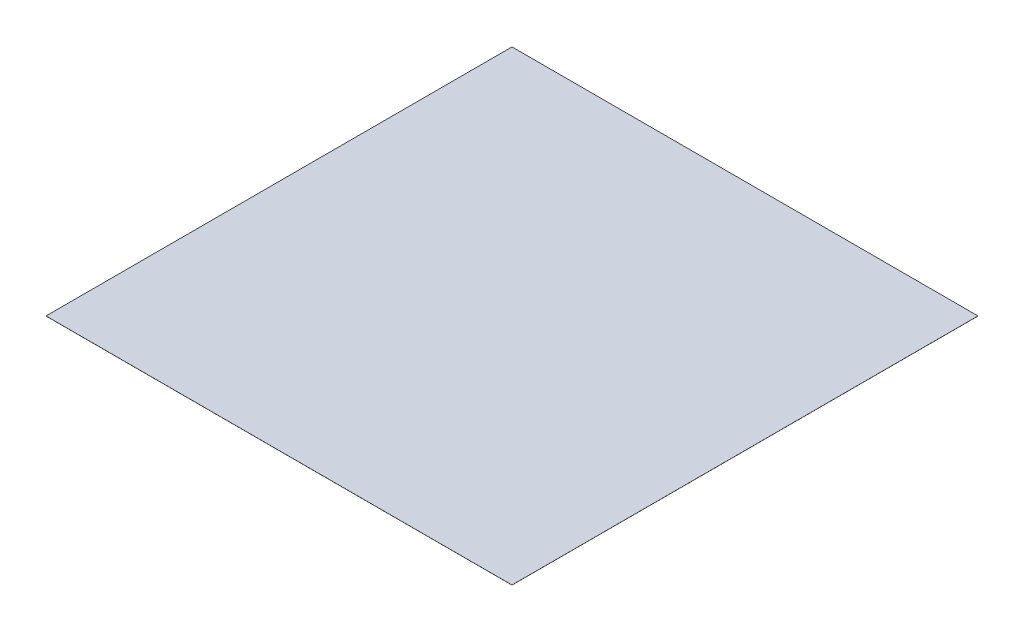
SolidWorks part; units mm, degrees
ref_plane "Front Plane" through (0, 0, 0) normal (0, 0, 1) x (1, 0, 0)
ref_plane "Top Plane" through (0, 0, 0) normal (0, 1, 0) x (1, 0, 0)
ref_plane "Right Plane" through (0, 0, 0) normal (1, 0, 0) x (0, 0, -1)
sketch "Sketch1" plane through (0, 0, 0) normal (0, 1, 0) x (1, 0, 0)
  line L1 (0, 0) -> (50000, 0)
  line L2 (0, 0) -> (0, 50000)
  line L3 (0, 50000) -> (50000, 50000)
  line L4 (50000, 0) -> (50000, 50000)
  dimension "D1" = 50000
  dimension "D2" = 50000
extrude "Boss-Extrude1" add sketch "Sketch1" along normal blind 10
